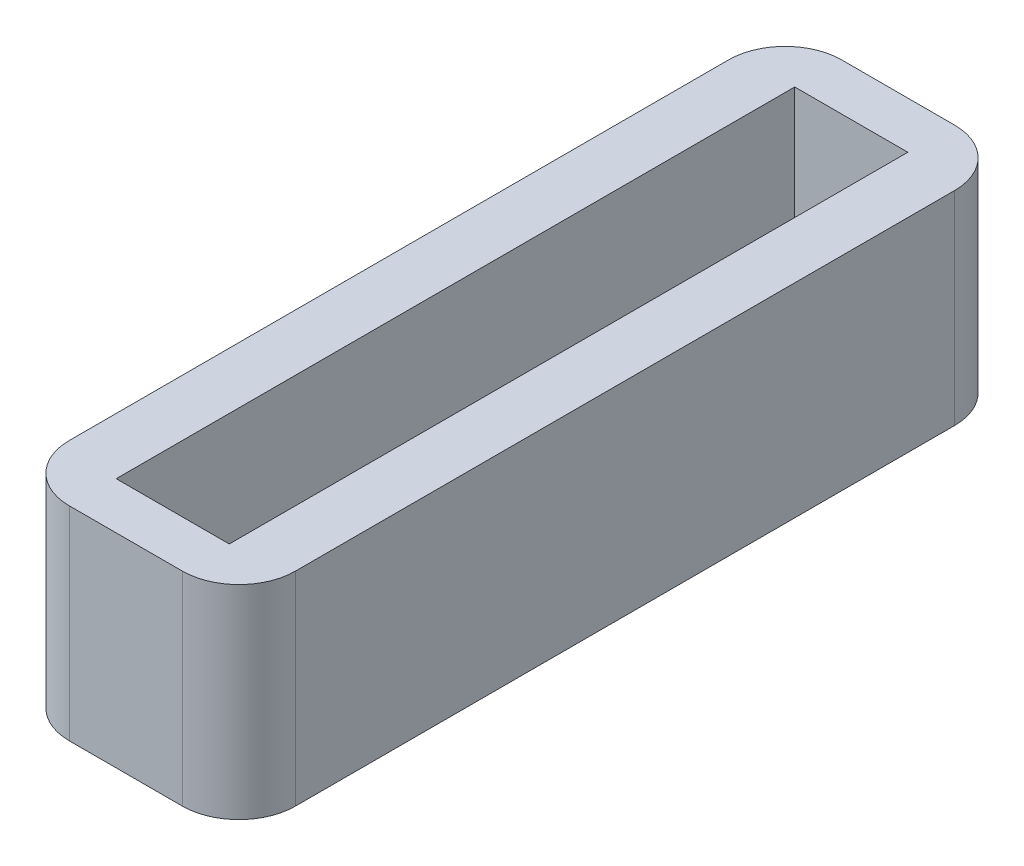
SolidWorks part; units mm, degrees
material "1060 Alloy"
ref_plane "Front Plane" through (0, 0, 0) normal (0, 0, 1) x (1, 0, 0)
ref_plane "Top Plane" through (0, 0, 0) normal (0, 1, 0) x (1, 0, 0)
ref_plane "Right Plane" through (0, 0, 0) normal (1, 0, 0) x (0, 0, -1)
sketch "Sketch2" plane through (0, 0, 0) normal (0, 0, 1) x (1, 0, 0)
  line L1 (-1, 1.7) -> (1, 1.7)
  line L2 (-1, 1.7) -> (-1, -1.7)
  line L3 (-1, -1.7) -> (1, -1.7)
  line L4 (1, 1.7) -> (1, -1.7)
  line L5 (-1, 1.7) -> (1, -1.7) construction
  line L6 (-1, -1.7) -> (1, 1.7) construction
  line L7 (-1.5, 2.175) -> (1.5, 2.175)
  line L8 (-1.5, 2.175) -> (-1.5, -2.175)
  line L9 (-1.5, -2.175) -> (1.5, -2.175)
  line L10 (1.5, 2.175) -> (1.5, -2.175)
  line L11 (-1.5, 2.175) -> (1.5, -2.175) construction
  line L12 (-1.5, -2.175) -> (1.5, 2.175) construction
  point P0 (0, 0)
  point P7 (0, 0)
sketch "Sketch3" plane through (0, 0, 0) normal (0, 1, 0) x (1, 0, 0)
  line L1 (-1, 6) -> (1, 6)
  line L2 (-1, 6) -> (-1, -6)
  line L3 (-1, -6) -> (1, -6)
  line L4 (1, 6) -> (1, -6)
  line L5 (-1, 6) -> (1, -6) construction
  line L6 (-1, -6) -> (1, 6) construction
  line L7 (-2, 6.8297) -> (2, 6.8297)
  line L8 (-2, 6.8297) -> (-2, -6.8297)
  line L9 (-2, -6.8297) -> (2, -6.8297)
  line L10 (2, 6.8297) -> (2, -6.8297)
  line L11 (-2, 6.8297) -> (2, -6.8297) construction
  line L12 (-2, -6.8297) -> (2, 6.8297) construction
  point P0 (0, 0)
  point P6 (0, 0)
extrude "Boss-Extrude3" add sketch "Sketch3" along normal blind 3.6
fillet "Fillet1" radius 1 4 edges at (-2, 1.8, -6.8297) (2, 1.8, -6.8297) (-2, 1.8, 6.8297) (2, 1.8, 6.8297)
